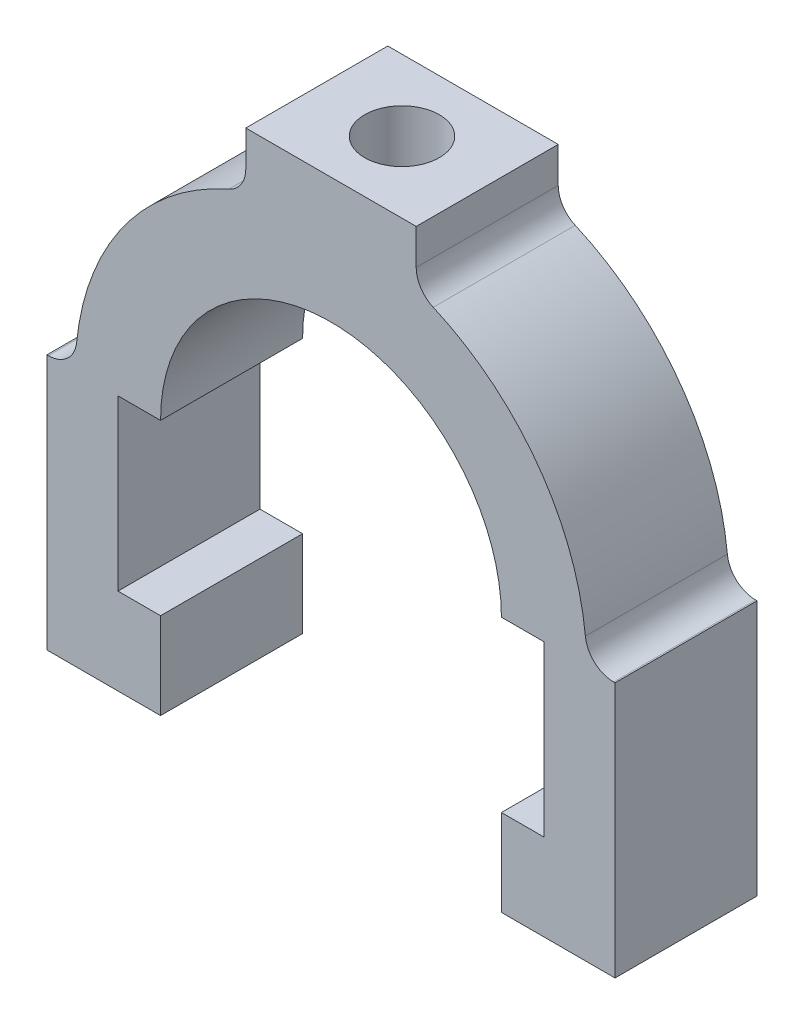
SolidWorks part; units mm, degrees
ref_plane "Ön Düzlem" through (0, 0, 0) normal (0, 0, 1) x (1, 0, 0)
ref_plane "Üst Düzlem" through (0, 0, 0) normal (0, 1, 0) x (1, 0, 0)
ref_plane "Sağ Düzlem" through (0, 0, 0) normal (1, 0, 0) x (0, 0, -1)
sketch "Çizim1" plane through (0, 0, 0) normal (0, 0, 1) x (1, 0, 0)
  line L0 (-41.2158, 0) -> (-36, 0) construction
  line L1 (39.7995, 0) -> (40, 0)
  line L2 (40, 0) -> (40, -36)
  line L3 (-39.7995, 0) -> (-40, 0)
  line L4 (-40, 0) -> (-40, -36)
  line L5 (30, 0) -> (30, -23.8167)
  line L6 (0, -7.3349) -> (0, 45.2502) construction
  line L7 (36, 0) -> (51.6541, 0) construction
  line L8 (-30, 0) -> (-30, -23.8167)
  line L9 (-30, 0) -> (-24, 0)
  line L10 (24, 0) -> (30, 0)
  line L11 (-40, -36) -> (-24, -36)
  line L12 (-24, -36) -> (-24, -23.8167)
  line L13 (-24, -23.8167) -> (-30, -23.8167)
  line L14 (40, -36) -> (24, -36)
  line L15 (24, -36) -> (24, -23.8167)
  line L16 (24, -23.8167) -> (30, -23.8167)
  line L17 (-30, 0) -> (30, 0) construction
  line L19 (-12, 41.6606) -> (12, 41.6606)
  line L20 (-12, 41.6606) -> (-12, 36.6606)
  line L22 (12, 41.6606) -> (12, 36.6606)
  arc A0 (24, 0) -> (-24, 0) centre (0, 0) ccw
  arc A1 (35.8195, 3.6) -> (14.4, 32.9945) centre (0, 0) ccw
  arc A2 (-14.4, 32.9945) -> (-35.8195, 3.6) centre (0, 0) ccw
  arc A3 (-35.8195, 3.6) -> (-39.7995, 0) centre (-39.7995, 4) cw
  arc A4 (-12, 36.6606) -> (-14.4, 32.9945) centre (-16, 36.6606) cw
  arc A5 (12, 36.6606) -> (14.4, 32.9945) centre (16, 36.6606) ccw
  arc A6 (35.8195, 3.6) -> (39.7995, 0) centre (39.7995, 4) ccw
  point P22 (0, 36)
  point P32 (-12, 33.9411)
  dimension "D1" = 72
  dimension "D2" = 48
  dimension "D11" = 4
  dimension "D3" = 4
  dimension "D4" = 80
  dimension "D5" = 10
  dimension "D6" = 10
  dimension "D7" = 36
  dimension "D8" = 16
  dimension "D9" = 24
  dimension "D10" = 12
  dimension "D12" = 5
extrude "Yükseklik-Ekstrüzyon1" add sketch "Çizim1" along normal blind 20
sketch "Çizim2" plane through (0, 41.6606, 0) normal (0, 1, 0) x (1, 0, 0)
  line L0 (-12, -20) -> (-12, 0) construction
  line L1 (12, 0) -> (-12, 0) construction
  circle A0 centre (0, -10) radius 5.2513
  dimension "D1" = 10
  dimension "D2" = 12
extrude "Kes-Ekstrüzyon1" cut sketch "Çizim2" against normal blind 35
